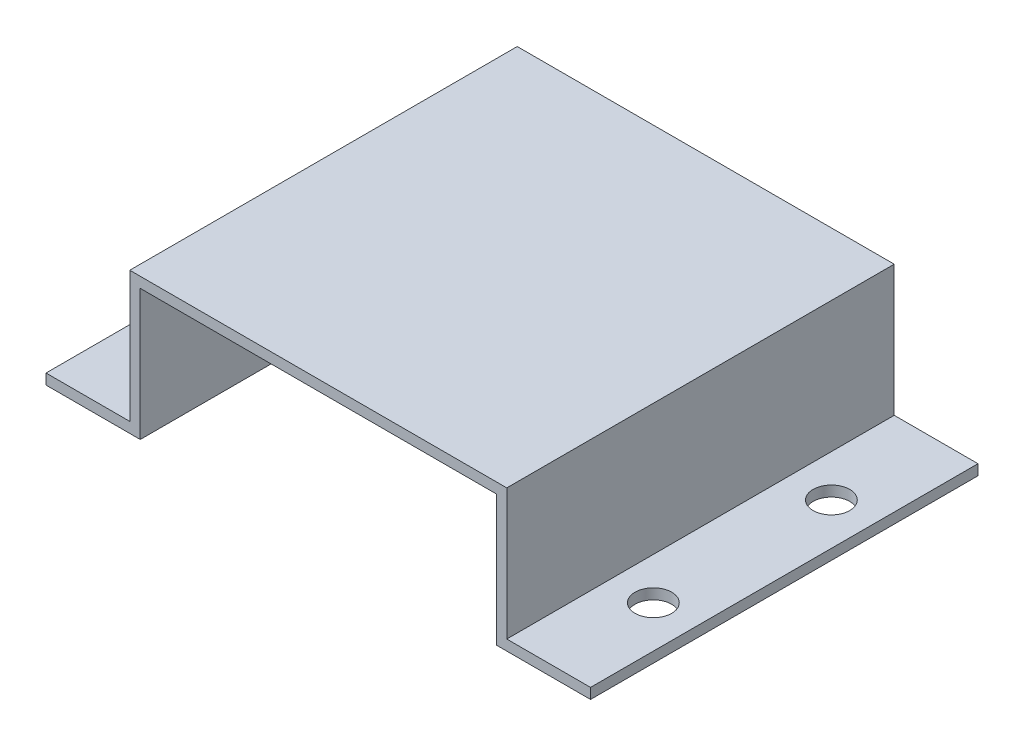
SolidWorks part; units mm, degrees
material "ABS PC"
ref_plane "Front Plane" through (0, 0, 0) normal (0, 0, 1) x (1, 0, 0)
ref_plane "Top Plane" through (0, 0, 0) normal (0, 1, 0) x (1, 0, 0)
ref_plane "Right Plane" through (0, 0, 0) normal (1, 0, 0) x (0, 0, -1)
sketch "Sketch1" plane through (0, 0, 0) normal (0, 0, 1) x (1, 0, 0)
  line L0 (0, 0) -> (0, 12.5)
  line L1 (0, 0) -> (-8, 0)
  line L2 (0, 12.5) -> (36, 12.5)
  line L3 (-8, 0) -> (-8, -1)
  line L4 (-8, -1) -> (1, -1)
  line L5 (1, -1) -> (1, 11.5)
  line L6 (1, 11.5) -> (35, 11.5)
  line L7 (36, 12.5) -> (36, 0)
  line L8 (36, 0) -> (44, 0)
  line L9 (44, 0) -> (44, -1)
  line L10 (44, -1) -> (35, -1)
  line L11 (35, 11.5) -> (35, -1)
  line L12 (1, -1) -> (-8, -1)
  dimension "D1" = 12.5
  dimension "D2" = 8
  dimension "D3" = 36
  dimension "D4" = 1
  dimension "D5" = 9
  dimension "D6" = 12.5
  dimension "D7" = 34
  dimension "D8" = 8
extrude "Boss-Extrude1" add sketch "Sketch1" along normal blind 37 contours L6 L11 L10 L9 L8 L7 L2 L0 L1 L3 L4 L5
sketch "Sketch2" plane through (0, 0, 0) normal (0, 1, 0) x (1, 0, 0)
  line L0 (-4, -37) -> (-4, -27)
  line L1 (0, -37) -> (-8, -37) construction
  line L2 (-4, 0) -> (-4, -10)
  line L3 (0, 0) -> (-8, 0) construction
  line L4 (40, -37) -> (40, -27)
  line L5 (36, -37) -> (44, -37) construction
  line L6 (40, 0) -> (40, -10)
  line L7 (36, 0) -> (44, 0) construction
  circle A0 centre (-4, -27) radius 1.75
  circle A1 centre (-4, -10) radius 1.75
  circle A2 centre (40, -27) radius 1.75
  circle A3 centre (40, -10) radius 1.75
  dimension "D3" = 3.5
  dimension "D4" = 3.5
  dimension "D5" = 3.5
  dimension "D6" = 3.5
  dimension "D1" = 10
  dimension "D2" = 10
extrude "Cut-Extrude1" cut sketch "Sketch2" against normal blind 6
